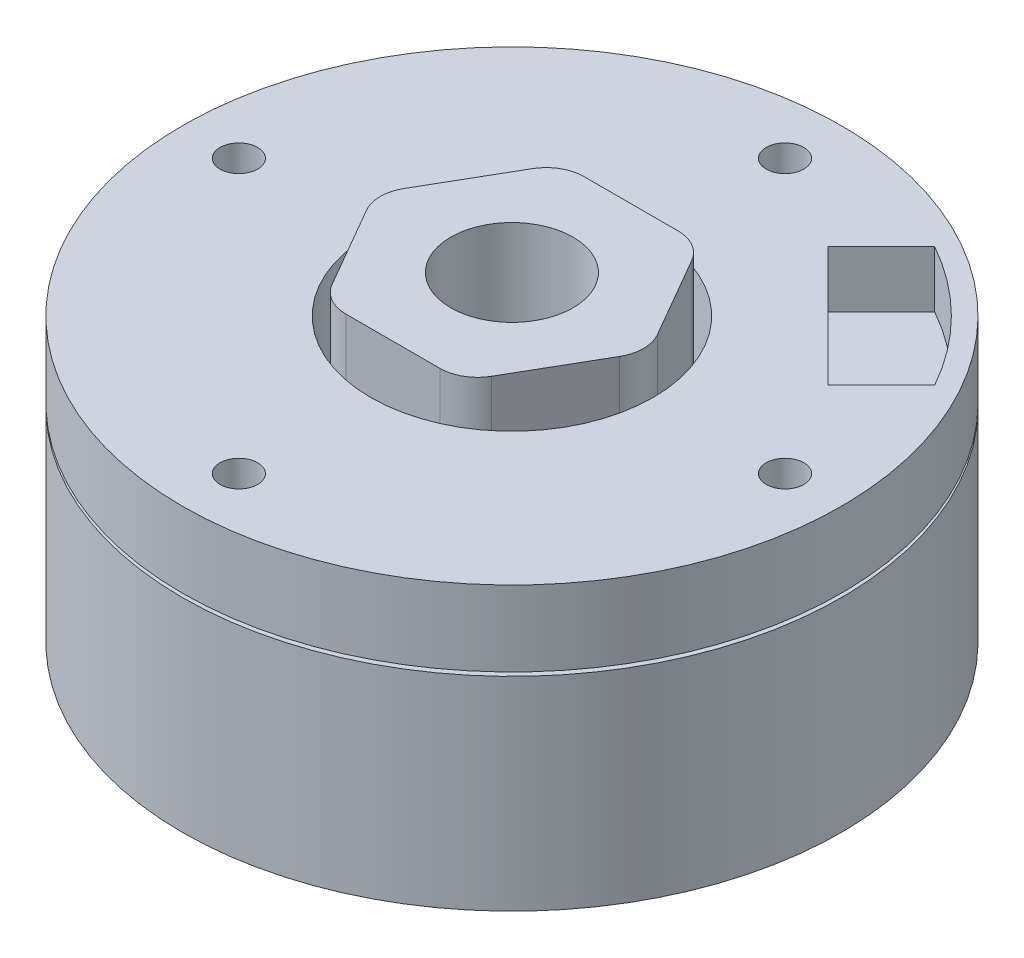
SolidWorks part; units mm, degrees
ref_plane "Front Plane" through (0, 0, 0) normal (0, 0, 1) x (1, 0, 0)
ref_plane "Top Plane" through (0, 0, 0) normal (0, 1, 0) x (1, 0, 0)
ref_plane "Right Plane" through (0, 0, 0) normal (1, 0, 0) x (0, 0, -1)
sketch "Sketch1" plane through (0, 0, 0) normal (0, 1, 0) x (1, 0, 0)
  circle A0 centre (0, 0) radius 17.5
  dimension "D1" = 35
extrude "Boss-Extrude1" add sketch "Sketch1" along normal blind 15
sketch "Sketch2" plane through (0, 15, 0) normal (0, 1, 0) x (1, 0, 0)
  line L1 (7.3, 0) -> (3.65, 6.322)
  line L2 (3.65, 6.322) -> (-3.65, 6.322)
  line L3 (-3.65, 6.322) -> (-7.3, 0)
  line L4 (-7.3, 0) -> (-3.65, -6.322)
  line L5 (-3.65, -6.322) -> (3.65, -6.322)
  line L6 (3.65, -6.322) -> (7.3, 0)
  circle A0 centre (0, 0) radius 6.322 construction
  circle A1 centre (0, 0) radius 7.5 construction
  dimension "D1" = 15
  dimension "D2" = 7.3
extrude "Boss-Extrude2" add sketch "Sketch2" along normal blind 2
sketch "Sketch3" plane through (0, 0, 0) normal (0, -1, 0) x (1, 0, 0)
  circle A0 centre (0, 0) radius 3.25
  dimension "D1" = 6.5
extrude "Cut-Extrude1" cut sketch "Sketch3" against normal up to next
sketch "Sketch4" plane through (0, 0, 0) normal (0, -1, 0) x (1, 0, 0)
  circle A0 centre (0, 9.5) radius 1
  point P2 (0, 0)
  dimension "D1" = 2
  dimension "D2" = 9.5
extrude "Cut-Extrude2" cut sketch "Sketch4" against normal blind 5
pattern_circular "CirPattern1" count 4 over 360 about axis through (0, 0, 0) along (0, 1, 0) of "Cut-Extrude2"
sketch "Sketch5" plane through (0, 15, 0) normal (0, 1, 0) x (1, 0, 0)
  circle A0 centre (0, 14.5) radius 1
  point P2 (0, 0)
  dimension "D1" = 2
  dimension "D2" = 14.5
extrude "Cut-Extrude3" cut sketch "Sketch5" against normal blind 2
pattern_circular "CirPattern2" count 4 over 360 about axis through (0, 0, 0) along (0, 1, 0) of "Cut-Extrude3"
sketch "Sketch6" plane through (0, 15, 0) normal (0, 1, 0) x (1, 0, 0)
  line L0 (7.3, 0) -> (3.65, 6.322) construction
  line L1 (7.3, 0) -> (3.65, 6.322)
  line L2 (3.65, 6.322) -> (-3.65, 6.322)
  line L3 (-3.65, 6.322) -> (-7.3, 0)
  line L4 (-7.3, 0) -> (-3.65, -6.322)
  line L5 (-3.65, -6.322) -> (3.65, -6.322)
  line L6 (3.65, -6.322) -> (7.3, 0)
  circle A0 centre (0, 0) radius 7.5
  circle A1 centre (0, 0) radius 6.322 construction
  dimension "D1" = 15
extrude "Cut-Extrude4" cut sketch "Sketch6" against normal blind 5
sketch "Sketch7" plane through (0, 15, 0) normal (0, 1, 0) x (1, 0, 0)
  circle A0 centre (0, 0) radius 17.5
  circle A1 centre (0, 0) radius 12.5
  circle A2 centre (0, 0) radius 17.5 construction
  dimension "D1" = 5
extrude "Cut-Extrude6" cut sketch "Sketch7" against normal blind 0.2 from offset 4 offset against normal yes
fillet "Fillet1" radius 2 6 edges at (-3.65, 13.5, 6.322) (-7.3, 13.5, 0) (-3.65, 13.5, -6.322) (3.65, 13.5, -6.322) (7.3, 13.5, 0) (3.65, 13.5, 6.322)
sketch "Sketch8" plane through (0, 15, 0) normal (0, 1, 0) x (1, 0, 0)
  line L0 (0, -1000) -> (0, 49000) construction
  line L1 (0, 0) -> (11.6673, 11.6673) construction
  line L2 (8.043, 14.407) -> (5.2146, 11.5785)
  line L3 (5.2146, 11.5785) -> (11.5785, 5.2146)
  line L4 (11.5785, 5.2146) -> (14.407, 8.043)
  circle A0 centre (0, 0) radius 16.5 construction
  circle A1 centre (0, 0) radius 17.5 construction
  arc A2 (14.407, 8.043) -> (8.043, 14.407) centre (0, 0) ccw
  point P10 (8.3965, 8.3965)
  point P14 (0, 0)
  dimension "D1" = 1
  dimension "D2" = 45
  dimension "D3" = 4
  dimension "D4" = 9
extrude "Cut-Extrude7" cut sketch "Sketch8" against normal blind 3
equation "\"D2@Sketch2\"=\"D1@Sketch2\"/2-0.2"
